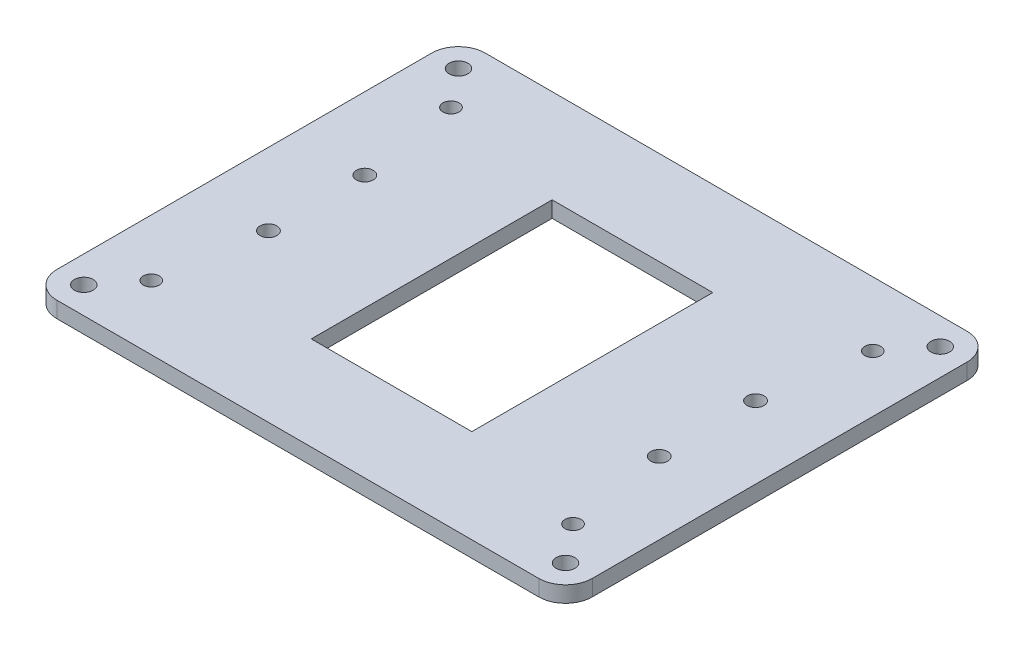
SolidWorks part; units mm, degrees
ref_plane "Front Plane" through (0, 0, 0) normal (0, 0, 1) x (1, 0, 0)
ref_plane "Top Plane" through (0, 0, 0) normal (0, 1, 0) x (1, 0, 0)
ref_plane "Right Plane" through (0, 0, 0) normal (1, 0, 0) x (0, 0, -1)
sketch "Sketch1" plane through (0, 0, 0) normal (0, 1, 0) x (1, 0, 0)
  line L1 (-45, 40) -> (45, 40)
  line L2 (-50, 35) -> (-50, -35)
  line L3 (-45, -40) -> (45, -40)
  line L4 (50, 35) -> (50, -35)
  line L5 (-50, 40) -> (50, -40) construction
  line L6 (-50, -40) -> (50, 40) construction
  arc A0 (45, 40) -> (50, 35) centre (45, 35) cw
  arc A1 (45, -40) -> (50, -35) centre (45, -35) ccw
  arc A2 (-50, -35) -> (-45, -40) centre (-45, -35) ccw
  arc A3 (-45, 40) -> (-50, 35) centre (-45, 35) ccw
  point P0 (0, 0)
  dimension "D3" = 5
  dimension "D1" = 100
  dimension "D2" = 80
extrude "Boss-Extrude1" add sketch "Sketch1" along normal blind 3
sketch "Sketch2" plane through (0, 3, 0) normal (0, 1, 0) x (1, 0, 0)
  line L0 (-103.2958, 0) -> (113.1301, 0) construction
  line L1 (0, 66.453) -> (0, -66.9993) construction
  line L2 (-50, 35) -> (-50, -35) construction
  circle A0 centre (-36.5, 9) radius 1.575
  circle A1 centre (-36.5, -9) radius 1.575
  circle A2 centre (36.5, -9) radius 1.575
  circle A3 centre (36.5, 9) radius 1.575
  dimension "D1" = 3.15
  dimension "D2" = 9
  dimension "D3" = 13.5
extrude "Cut-Extrude1" cut sketch "Sketch2" against normal blind 4
sketch "Sketch3" plane through (0, 3, 0) normal (0, 1, 0) x (1, 0, 0)
  line L0 (-45, -40) -> (45, -40) construction
  line L1 (-50, 35) -> (-50, -35) construction
  circle A0 centre (-45, -35) radius 1.75
  dimension "D1" = 3.5
  dimension "D2" = 5
  dimension "D3" = 5
extrude "Cut-Extrude2" cut sketch "Sketch3" against normal through all
pattern_linear "LPattern1" count 2 spacing 70 along (0, 0, -1) count 2 spacing 90 along (1, 0, 0) of "Cut-Extrude2"
sketch "Sketch4" plane through (0, 3, 0) normal (0, 1, 0) x (1, 0, 0)
  line L0 (-59.0941, 0) -> (68.8899, 0) construction
  line L1 (-39.4, 28) -> (39.4, 28) construction
  line L2 (-39.4, 28) -> (-39.4, -28) construction
  line L3 (-39.4, -28) -> (39.4, -28) construction
  line L4 (39.4, 28) -> (39.4, -28) construction
  line L5 (-39.4, 28) -> (39.4, -28) construction
  line L6 (-39.4, -28) -> (39.4, 28) construction
  line L7 (0, 42.0047) -> (0, -43.6019) construction
  circle A0 centre (-39.4, 28) radius 1.5
  circle A1 centre (39.4, 28) radius 1.5
  circle A2 centre (39.4, -28) radius 1.5
  circle A3 centre (-39.4, -28) radius 1.5
  point P0 (0, 0)
  dimension "D3" = 3
  dimension "D1" = 78.8
  dimension "D2" = 56
extrude "Cut-Extrude3" cut sketch "Sketch4" against normal through all
sketch "Sketch5" plane through (0, 3, 0) normal (0, 1, 0) x (1, 0, 0)
  line L1 (-15, 22.5) -> (15, 22.5)
  line L2 (-15, 22.5) -> (-15, -22.5)
  line L3 (-15, -22.5) -> (15, -22.5)
  line L4 (15, 22.5) -> (15, -22.5)
  line L5 (-15, 22.5) -> (15, -22.5) construction
  line L6 (-15, -22.5) -> (15, 22.5) construction
  point P0 (0, 0)
  dimension "D1" = 45
  dimension "D2" = 30
extrude "Cut-Extrude4" cut sketch "Sketch5" against normal through all
